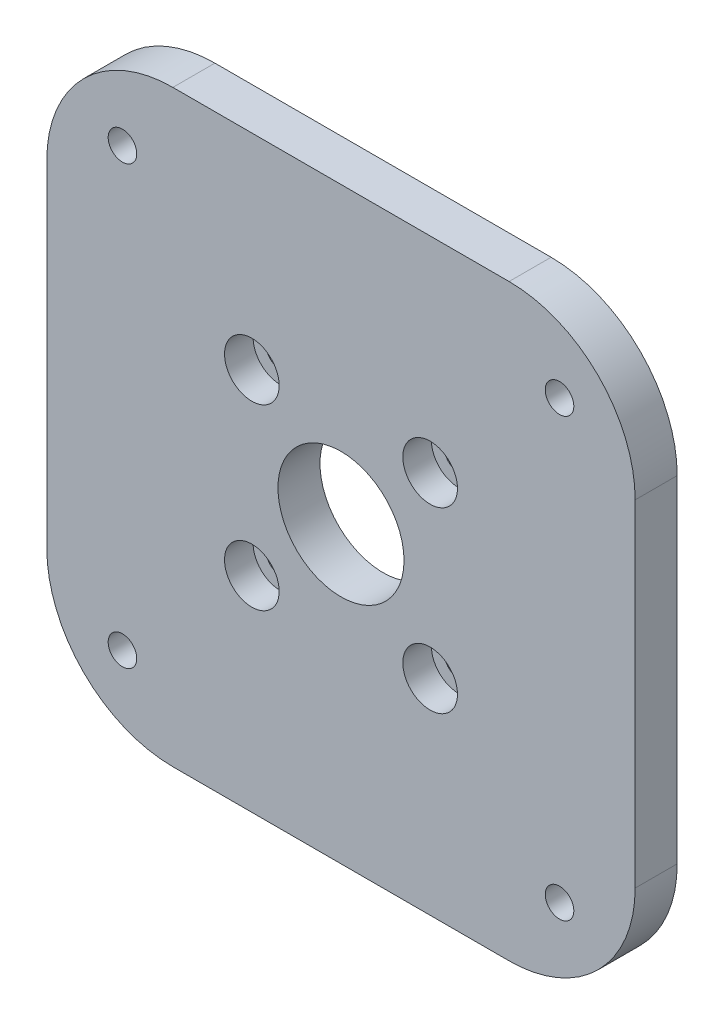
SolidWorks part; units mm, degrees
ref_plane "Front Plane" through (0, 0, 0) normal (0, 0, 1) x (1, 0, 0)
ref_plane "Top Plane" through (0, 0, 0) normal (0, 1, 0) x (1, 0, 0)
ref_plane "Right Plane" through (0, 0, 0) normal (1, 0, 0) x (0, 0, -1)
sketch "Sketch1" plane through (0, 0, 0) normal (0, 0, 1) x (1, 0, 0)
  line L1 (-35, 35) -> (35, 35)
  line L2 (-35, 35) -> (-35, -35)
  line L3 (-35, -35) -> (35, -35)
  line L4 (35, 35) -> (35, -35)
  line L5 (-35, 35) -> (35, -35) construction
  line L6 (-35, -35) -> (35, 35) construction
  point P0 (0, 0)
  dimension "D2" = 70
extrude "Boss-Extrude1" add sketch "Sketch1" along normal blind 5
fillet "Fillet1" radius 15 4 edges at (-35, -35, 2.5) (-35, 35, 2.5) (35, 35, 2.5) (35, -35, 2.5)
hole_wizard "CBORE for M3 Hex Socket Head Cap Screw1" positions "Sketch4" profile "Sketch3" counterbore size "M3" standard "ISO" end condition through all
sketch "Sketch4" plane through (0, 0, 5) normal (0, 0, 1) x (1, 0, 0)
  line L0 (-20, -35) -> (20, -35) construction
  line L1 (-35, 20) -> (-35, -20) construction
  line L2 (20, 35) -> (-20, 35) construction
  point P0 (-10.6066, -10.6066)
  point P2 (-10.6066, 10.6066)
  point P4 (10.6066, 10.6066)
  point P6 (10.6066, -10.6066)
  dimension "D1" = 24.3934
  dimension "D2" = 24.3934
  dimension "D3" = 24.3934
  dimension "D4" = 24.3934
  dimension "D5" = 21.2132
  dimension "D6" = 21.2132
  dimension "D7" = 24.3934
  dimension "D8" = 21.2132
sketch "Sketch3" plane through (-10.6066, -10.6066, 5) normal (1, 0, 0) x (0, -1, 0)
  line L0 (0, 0) -> (0, 5)
  line L1 (0, 5) -> (1.7, 5)
  line L3 (1.7, 5) -> (1.7, 3.4)
  line L4 (1.7, 3.4) -> (3.25, 3.4)
  line L5 (3.25, 3.4) -> (3.25, 0)
  line L7 (3.25, 0) -> (0, 0)
  line L11 (0, -6.35) -> (0, 107.95) construction
  dimension "Thru Hole Dia." = 3.4
  dimension "Thru Hole Depth" = 5
  dimension "C'Bore Dia." = 6.5
  dimension "C'Bore Depth" = 3.4
sketch "Sketch5" plane through (0, 0, 5) normal (0, 0, 1) x (1, 0, 0)
  circle A0 centre (0, 0) radius 7.5
  dimension "D1" = 15
extrude "Cut-Extrude1" cut sketch "Sketch5" against normal through all
hole_wizard "M3 Clearance Hole1" positions "Sketch6" profile "Sketch7" hole size "M3" standard "ISO" end condition through all
sketch "Sketch6" plane through (0, 0, 5) normal (0, 0, 1) x (1, 0, 0)
  line L0 (-35, 20) -> (-35, -20) construction
  line L2 (20, 35) -> (-20, 35) construction
  point P0 (26, 26)
  point P2 (-26, 26)
  point P4 (-26, -26)
  point P6 (26, -26)
  dimension "D1" = 9
  dimension "D2" = 9
  dimension "D3" = 52
  dimension "D4" = 52
  dimension "D5" = 52
sketch "Sketch7" plane through (26, 26, 5) normal (1, 0, 0) x (0, -1, 0)
  line L0 (0, 0) -> (0, 5)
  line L1 (0, 5) -> (1.7, 5)
  line L2 (1.7, 5) -> (1.7, 0)
  line L5 (1.7, 0) -> (0, 0)
  line L11 (0, -6.35) -> (0, 107.95) construction
  dimension "Thru Hole Dia." = 3.4
  dimension "Thru Hole Depth" = 5
